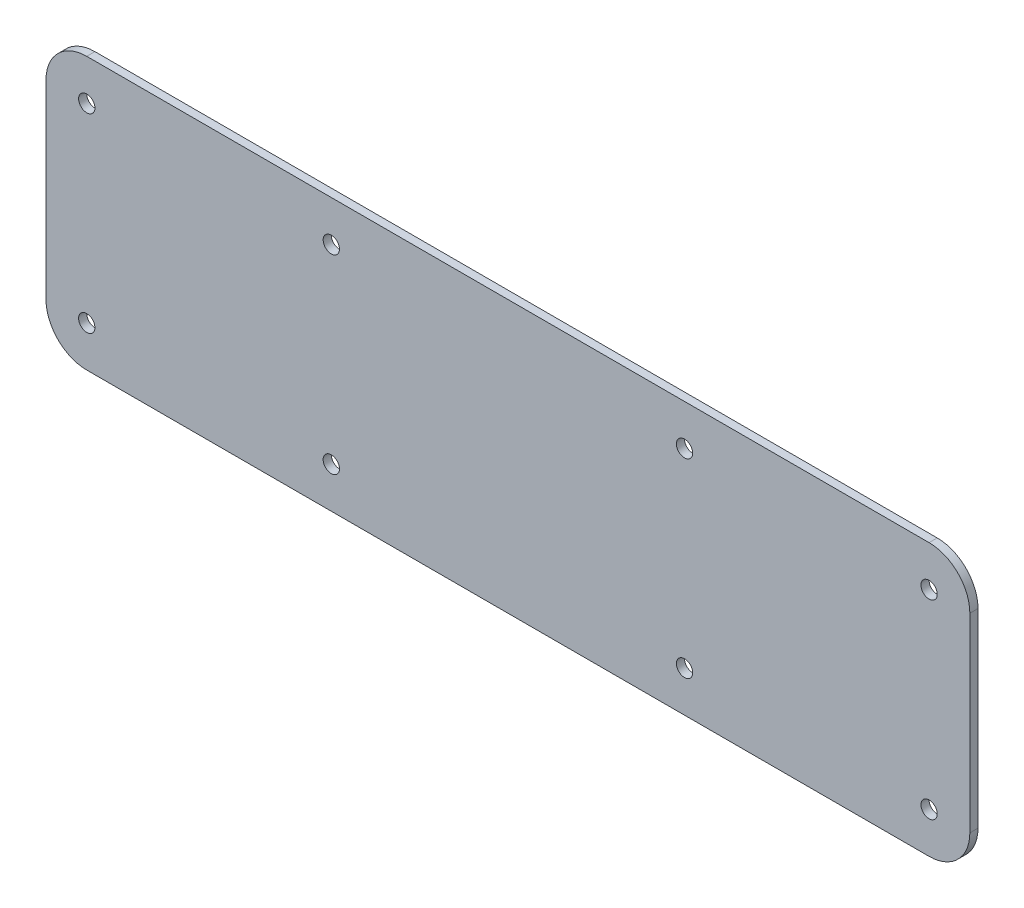
SolidWorks part; units mm, degrees
ref_plane "Front Plane" through (0, 0, 0) normal (0, 0, 1) x (1, 0, 0)
ref_plane "Top Plane" through (0, 0, 0) normal (0, 1, 0) x (1, 0, 0)
ref_plane "Right Plane" through (0, 0, 0) normal (1, 0, 0) x (0, 0, -1)
sketch "Sketch1" plane through (0, 0, 0) normal (0, 0, 1) x (1, 0, 0)
  line L0 (0, 0) -> (0, 17.5) construction
  line L1 (0, 17.5) -> (25, 17.5) construction
  line L2 (25, 17.5) -> (40, 17.5) construction
  line L3 (40, 17.5) -> (70, 17.5) construction
  line L4 (70, 17.5) -> (77.5, 17.5) construction
  line L5 (0, 17.5) -> (-25, 17.5) construction
  line L6 (-25, 17.5) -> (-40, 17.5) construction
  line L7 (-70, 17.5) -> (-77.5, 17.5) construction
  line L8 (-40, 17.5) -> (-70, 17.5) construction
  line L9 (-77.5, 17.5) -> (-77.5, -17.5) construction
  line L10 (-77.5, -25) -> (77.5, -25)
  line L11 (-85, -17.5) -> (-85, 17.5)
  line L12 (-77.5, 25) -> (77.5, 25)
  line L13 (85, -17.5) -> (85, 17.5)
  line L14 (-85, -25) -> (85, 25) construction
  line L15 (-85, 25) -> (85, -25) construction
  circle A0 centre (-32.5, 17.5) radius 1.5
  circle A1 centre (32.5, 17.5) radius 1.5
  circle A2 centre (77.5, 17.5) radius 1.5
  circle A3 centre (-77.5, 17.5) radius 1.5
  circle A4 centre (-77.5, -17.5) radius 1.5
  circle A5 centre (-32.5, -17.5) radius 1.5
  circle A6 centre (32.5, -17.5) radius 1.5
  circle A7 centre (77.5, -17.5) radius 1.5
  arc A8 (77.5, 25) -> (85, 17.5) centre (77.5, 17.5) cw
  arc A9 (77.5, -25) -> (85, -17.5) centre (77.5, -17.5) ccw
  arc A10 (-77.5, -25) -> (-85, -17.5) centre (-77.5, -17.5) cw
  arc A11 (-85, 17.5) -> (-77.5, 25) centre (-77.5, 17.5) cw
  dimension "D1" = 7.5
extrude "Boss-Extrude1" add sketch "Sketch1" along normal blind 1.5
